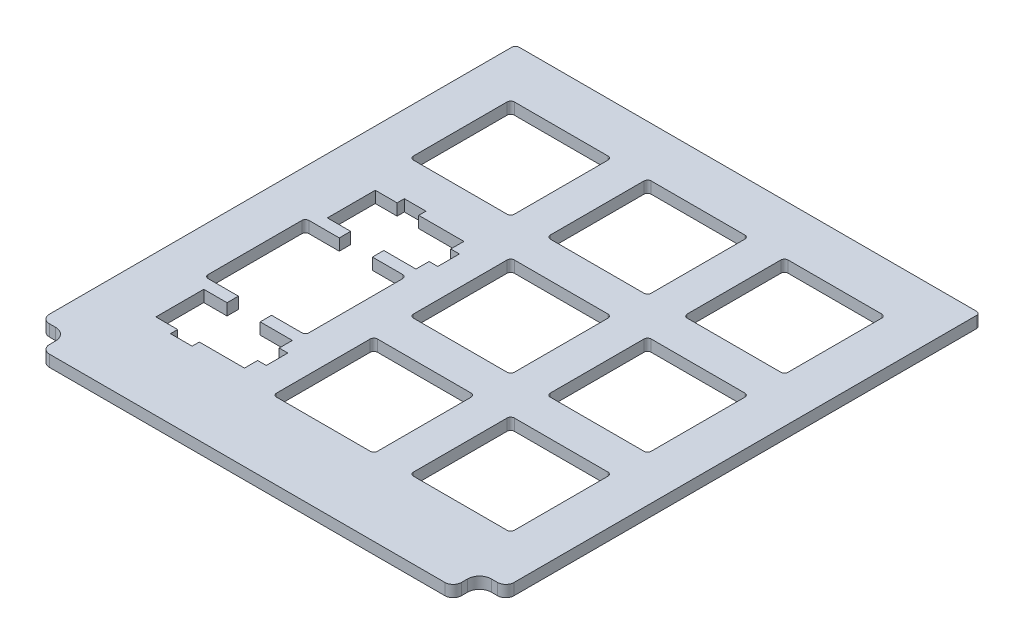
SolidWorks part; units mm, degrees
ref_plane "前视基准面" through (0, 0, 0) normal (0, 0, 1) x (1, 0, 0)
ref_plane "上视基准面" through (0, 0, 0) normal (0, 1, 0) x (1, 0, 0)
ref_plane "右视基准面" through (0, 0, 0) normal (1, 0, 0) x (0, 0, -1)
sketch "草图1" plane through (0, 0, 0) normal (0, 1, 0) x (1, 0, 0)
  line L0 (-12.5008, 61.2283) -> (51.9992, 61.2283)
  line L5 (51.9992, 61.2283) -> (51.9992, -3.4717)
  line L6 (-12.5008, 61.2283) -> (-12.5008, -3.4717)
  line L19 (50.8492, 119.1658) -> (49.9992, 119.1658)
  line L20 (48.3492, 120.8158) -> (48.3492, 121.6658)
  line L21 (47.1992, 122.8158) -> (-7.7008, 122.8158)
  line L22 (-8.8508, 121.6658) -> (-8.8508, 120.8158)
  line L23 (-10.5008, 119.1658) -> (-11.3508, 119.1658)
  line L24 (-12.5008, 118.0158) -> (-12.5008, -3.4717)
  line L25 (-11.3508, -4.6217) -> (-10.5008, -4.6217)
  line L26 (-8.8508, -6.2717) -> (-8.8508, -7.1217)
  line L27 (-7.7008, -8.2717) -> (47.1992, -8.2717)
  line L28 (48.3492, -7.1217) -> (48.3492, -6.2717)
  line L29 (49.9992, -4.6217) -> (50.8492, -4.6217)
  line L30 (51.9992, -3.4717) -> (51.9992, 97.2055)
  line L37 (-11.3508, -4.6217) -> (-10.5008, -4.6217)
  line L38 (-8.8508, -6.2717) -> (-8.8508, -7.1217)
  line L39 (-7.7008, -8.2717) -> (47.1992, -8.2717)
  line L40 (48.3492, -7.1217) -> (48.3492, -6.2717)
  line L41 (49.9992, -4.6217) -> (50.8492, -4.6217)
  line L266 (50.9992, 117.4055) -> (51.9992, 117.4055)
  line L268 (51.9992, 117.4055) -> (51.9992, 118.0158)
  line L270 (51.9992, 97.2055) -> (50.9992, 97.2055)
  line L272 (50.9992, 97.2055) -> (50.9992, 117.4055)
  arc A14 (51.9992, 118.0158) -> (50.8492, 119.1658) centre (50.8492, 118.0158) ccw
  arc A15 (48.3492, 120.8158) -> (49.9992, 119.1658) centre (49.9992, 120.8158) ccw
  arc A16 (48.3492, 121.6658) -> (47.1992, 122.8158) centre (47.1992, 121.6658) ccw
  arc A17 (-7.7008, 122.8158) -> (-8.8508, 121.6658) centre (-7.7008, 121.6658) ccw
  arc A18 (-10.5008, 119.1658) -> (-8.8508, 120.8158) centre (-10.5008, 120.8158) ccw
  arc A19 (-11.3508, 119.1658) -> (-12.5008, 118.0158) centre (-11.3508, 118.0158) ccw
  arc A20 (-12.5008, -3.4717) -> (-11.3508, -4.6217) centre (-11.3508, -3.4717) ccw
  arc A21 (-8.8508, -6.2717) -> (-10.5008, -4.6217) centre (-10.5008, -6.2717) ccw
  arc A22 (-8.8508, -7.1217) -> (-7.7008, -8.2717) centre (-7.7008, -7.1217) ccw
  arc A23 (47.1992, -8.2717) -> (48.3492, -7.1217) centre (47.1992, -7.1217) ccw
  arc A24 (49.9992, -4.6217) -> (48.3492, -6.2717) centre (49.9992, -6.2717) ccw
  arc A25 (50.8492, -4.6217) -> (51.9992, -3.4717) centre (50.8492, -3.4717) ccw
  arc A32 (-12.5008, -3.4717) -> (-11.3508, -4.6217) centre (-11.3508, -3.4717) ccw
  arc A33 (-8.8508, -6.2717) -> (-10.5008, -4.6217) centre (-10.5008, -6.2717) ccw
  arc A34 (-8.8508, -7.1217) -> (-7.7008, -8.2717) centre (-7.7008, -7.1217) ccw
  arc A35 (47.1992, -8.2717) -> (48.3492, -7.1217) centre (47.1992, -7.1217) ccw
  arc A36 (49.9992, -4.6217) -> (48.3492, -6.2717) centre (49.9992, -6.2717) ccw
  arc A37 (50.8492, -4.6217) -> (51.9992, -3.4717) centre (50.8492, -3.4717) ccw
  dimension "D2" = 69.5
  dimension "D1" = 0
extrude "凸台-拉伸1" add sketch "草图1" along normal blind 1.6
sketch "草图2" plane through (0, 0, 0) normal (0, -1, 0) x (1, 0, 0)
  line L0 (19.7492, 25.7738) -> (19.7492, -89.1768) construction
  line L1 (-22.8684, -28.3158) -> (51.3053, -28.3158) construction
  line L5 (-9.5008, -57.5658) -> (48.9992, -57.5658)
  line L6 (-9.5008, 0.9342) -> (-9.5008, -57.5658)
  line L7 (48.9992, 0.9342) -> (-9.5008, 0.9342)
  line L8 (48.9992, -57.5658) -> (48.9992, 0.9342)
  line L9 (-9.5008, -57.5658) -> (48.9992, -57.5658) construction
  line L10 (-9.5008, 0.9342) -> (-9.5008, -57.5658) construction
  line L11 (48.9992, 0.9342) -> (-9.5008, 0.9342) construction
  line L12 (48.9992, -57.5658) -> (48.9992, 0.9342) construction
  line L16 (45.7492, -16.3158) -> (31.7492, -16.3158)
  line L37 (45.7492, -16.3158) -> (45.7492, -2.3158)
  line L38 (45.7492, -2.3158) -> (31.7492, -2.3158)
  line L39 (31.7492, -16.3158) -> (31.7492, -2.3158)
  line L40 (45.7492, -16.3158) -> (31.7492, -2.3158) construction
  line L41 (45.7492, -2.3158) -> (31.7492, -16.3158) construction
  point P4 (38.7492, -9.3158)
  dimension "D2" = 14
  dimension "D3" = 19
  dimension "D4" = 19
  dimension "D1" = 0
extrude "切除-拉伸1" cut sketch "草图2" against normal up to next (1.6 mm away)
fillet "圆角1" radius 0.5 4 edges at (45.7492, 0.8, -2.3158) (31.7492, 0.8, -2.3158) (31.7492, 0.8, -16.3158) (45.7492, 0.8, -16.3158)
pattern_linear "阵列(线性)2" count 3 spacing 19 along (0, 0, -1) count 3 spacing 19 along (-1, 0, 0) skipping (0, 2), (1, 2) of "圆角1", "切除-拉伸1"
sketch "草图3" plane through (0, 1.6, 0) normal (0, 1, 0) x (1, 0, 0)
  line L0 (-24.3873, 18.8158) -> (58.3219, 18.8158) construction
  line L1 (0.7492, -13.1729) -> (0.7492, 58.2769) construction
  line L2 (-6.2508, 12.3158) -> (-6.2508, 25.3158)
  line L3 (7.7492, 25.3158) -> (7.7492, 12.3158)
  line L4 (-5.7508, 25.8158) -> (-1.5508, 25.8158)
  line L9 (-6.2508, 25.8158) -> (7.7492, 11.8158) construction
  line L10 (-6.2508, 11.8158) -> (7.7492, 25.8158) construction
  line L11 (-1.5508, 25.8158) -> (-1.5508, 27.3958)
  line L12 (-4.7808, 27.3958) -> (-1.5508, 27.3958)
  line L13 (-4.7808, 27.3958) -> (-4.7808, 34.0458)
  line L14 (-4.7808, 34.0458) -> (-1.7508, 34.0458)
  line L15 (-1.7508, 34.0458) -> (-1.7508, 35.0458)
  line L16 (-1.7508, 35.0458) -> (1.2492, 35.0458)
  line L17 (1.2492, 35.0458) -> (1.2492, 34.0458)
  line L18 (1.2492, 34.0458) -> (7.5192, 34.0458)
  line L19 (7.5192, 34.0458) -> (7.5192, 32.2208)
  line L20 (7.5192, 32.2208) -> (8.7192, 32.2208)
  line L21 (8.7192, 32.2208) -> (8.7192, 29.2208)
  line L22 (8.7192, 29.2208) -> (7.5192, 29.2208)
  line L23 (7.5192, 29.2208) -> (7.5192, 27.3958)
  line L24 (7.5192, 27.3958) -> (3.0492, 27.3958)
  line L25 (3.0492, 27.3958) -> (3.0492, 25.8158)
  line L26 (3.0492, 25.8158) -> (7.2492, 25.8158)
  line L27 (3.0492, 11.8158) -> (7.2492, 11.8158)
  line L28 (3.0492, 10.2358) -> (3.0492, 11.8158)
  line L29 (7.5192, 10.2358) -> (3.0492, 10.2358)
  line L30 (7.5192, 8.4108) -> (7.5192, 10.2358)
  line L31 (8.7192, 8.4108) -> (7.5192, 8.4108)
  line L32 (8.7192, 5.4108) -> (8.7192, 8.4108)
  line L33 (7.5192, 5.4108) -> (8.7192, 5.4108)
  line L34 (7.5192, 3.5858) -> (7.5192, 5.4108)
  line L35 (1.2492, 3.5858) -> (7.5192, 3.5858)
  line L36 (1.2492, 2.5858) -> (1.2492, 3.5858)
  line L37 (-1.7508, 2.5858) -> (1.2492, 2.5858)
  line L38 (-1.7508, 3.5858) -> (-1.7508, 2.5858)
  line L39 (-4.7808, 3.5858) -> (-1.7508, 3.5858)
  line L40 (-4.7808, 10.2358) -> (-4.7808, 3.5858)
  line L41 (-4.7808, 10.2358) -> (-1.5508, 10.2358)
  line L42 (-1.5508, 11.8158) -> (-1.5508, 10.2358)
  line L43 (-5.7508, 11.8158) -> (-1.5508, 11.8158)
  arc A0 (-6.2508, 25.3158) -> (-5.7508, 25.8158) centre (-5.7508, 25.3158) cw
  arc A1 (7.2492, 25.8158) -> (7.7492, 25.3158) centre (7.2492, 25.3158) cw
  arc A2 (7.2492, 11.8158) -> (7.7492, 12.3158) centre (7.2492, 12.3158) ccw
  arc A3 (-6.2508, 12.3158) -> (-5.7508, 11.8158) centre (-5.7508, 12.3158) ccw
  point P4 (0.7492, 18.8158)
  point P5 (0.7492, 18.8158)
  dimension "D1" = 14
  dimension "D2" = 4.2
  dimension "D3" = 1.58
  dimension "D4" = 3.23
  dimension "D5" = 6.65
  dimension "D6" = 3.03
  dimension "D7" = 3
  dimension "D8" = 1
  dimension "D9" = 6.27
  dimension "D10" = 3
  dimension "D11" = 1.2
  dimension "D12" = 0.5
  dimension "D13" = 13
  dimension "D14" = 45
  dimension "D15" = 4.47
extrude "切除-拉伸3" cut sketch "草图3" against normal up to surface (1.6 mm away) up to face at (38.7492, 0, -28.3158)
fillet "圆角2" radius 0.5 2 edges at (51.9992, 0.8, -61.2283) (-12.5008, 0.8, -61.2283)
